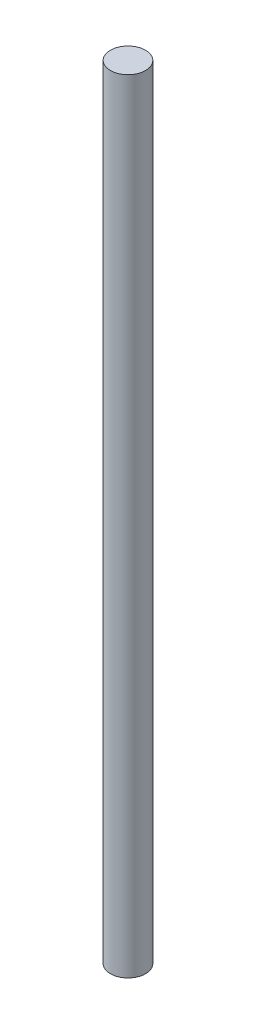
SolidWorks part; units mm, degrees
ref_plane "Front Plane" through (0, 0, 0) normal (0, 0, 1) x (1, 0, 0)
ref_plane "Top Plane" through (0, 0, 0) normal (0, 1, 0) x (1, 0, 0)
ref_plane "Right Plane" through (0, 0, 0) normal (1, 0, 0) x (0, 0, -1)
sketch "Sketch1" plane through (0, 0, 0) normal (0, 1, 0) x (1, 0, 0)
  circle A0 centre (0, 0) radius 3.19
extrude "Boss-Extrude1" add sketch "Sketch1" along normal blind 142 contours A0
